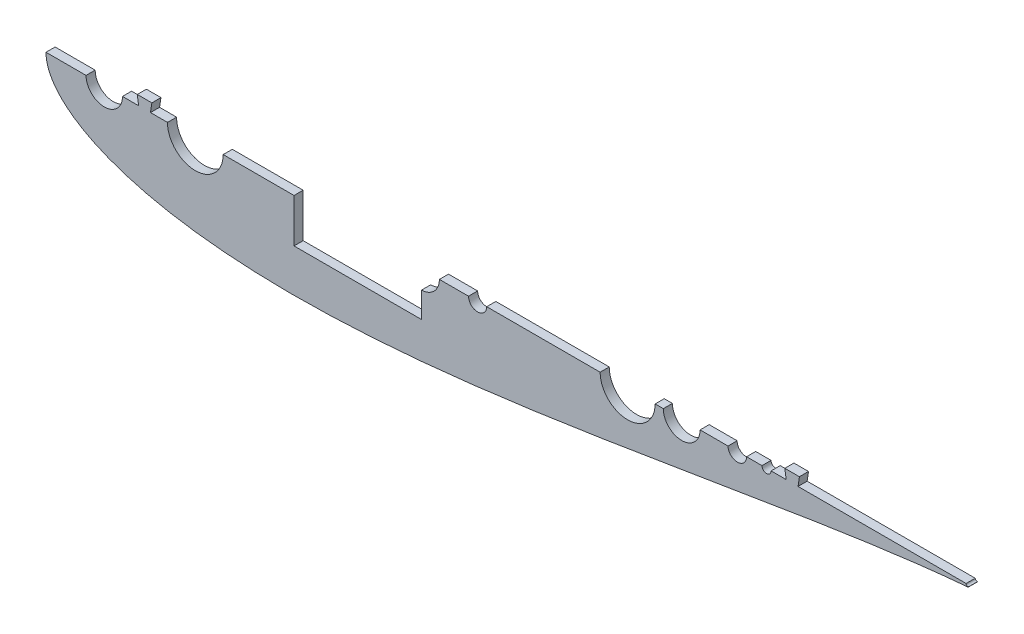
SolidWorks part; units mm, degrees
material "Beech"
ref_plane "Front Plane" through (0, 0, 0) normal (0, 0, 1) x (1, 0, 0)
ref_plane "Top Plane" through (0, 0, 0) normal (0, 1, 0) x (1, 0, 0)
ref_plane "Right Plane" through (0, 0, 0) normal (1, 0, 0) x (0, 0, -1)
curve "Curve4"
  spline degree 3 poles (100, 0, 0) (99.8498, 0.0023, 0) (99.4759, 0.008, 0) (99.1023, 0.0238, 0) (98.8789, 0.0332, 0) knots 0 0 0 0 0.401829 1 1 1 1
curve "Curve5"
  spline degree 3 poles (99.3714, -0.0082, 0) (100.2526, 0, 0) (99.3714, 0.0082, 0) (98.8504, 0.035, 0) (97.904, 0.0811, 0) (96.8285, 0.1543, 0) (95.5159, 0.2583, 0) (94.013, 0.3972, 0) (92.313, 0.574, 0) (90.4281, 0.791, 0) (88.3655, 1.0495, 0) (86.1348, 1.3497, 0) (83.7456, 1.691, 0) (81.2082, 2.0715, 0) (78.5335, 2.4886, 0) (75.7326, 2.9386, 0) (72.8172, 3.4168, 0) (69.799, 3.9177, 0) (66.6904, 4.435, 0) (63.5039, 4.9616, 0) (60.2521, 5.4899, 0) (56.948, 6.0119, 0) (53.6049, 6.519, 0) (50.2363, 7.0024, 0) (46.8558, 7.4534, 0) (43.4774, 7.8632, 0) (40.1152, 8.2232, 0) (36.7837, 8.5249, 0) (33.4975, 8.7606, 0) (30.2716, 8.923, 0) (27.1211, 9.0055, 0) (24.0614, 9.0025, 0) (21.108, 8.909, 0) (18.277, 8.7213, 0) (15.5843, 8.4369, 0) (13.0466, 8.0543, 0) (10.6806, 7.5735, 0) (8.5039, 6.996, 0) (6.5349, 6.3253, 0) (4.7933, 5.5673, 0) (3.3001, 4.7321, 0) (2.0777, 3.8366, 0) (1.1467, 2.91, 0) (0.5165, 2.0014, 0) (0.165, 1.1816, 0) (0.0231, 0.524, 0) (-0.0093, 0, 0) (0.0231, -0.524, 0) (0.165, -1.1816, 0) (0.5165, -2.0014, 0) (1.1467, -2.91, 0) (2.0777, -3.8366, 0) (3.3001, -4.7321, 0) (4.7933, -5.5673, 0) (6.5349, -6.3253, 0) (8.5039, -6.996, 0) (10.6806, -7.5735, 0) (13.0466, -8.0543, 0) (15.5843, -8.4369, 0) (18.277, -8.7213, 0) (21.108, -8.909, 0) (24.0614, -9.0025, 0) (27.1211, -9.0055, 0) (30.2716, -8.923, 0) (33.4975, -8.7606, 0) (36.7837, -8.5249, 0) (40.1152, -8.2232, 0) (43.4774, -7.8632, 0) (46.8558, -7.4534, 0) (50.2363, -7.0024, 0) (53.6049, -6.519, 0) (56.948, -6.0119, 0) (60.2521, -5.4899, 0) (63.5039, -4.9616, 0) (66.6904, -4.435, 0) (69.799, -3.9177, 0) (72.8172, -3.4168, 0) (75.7326, -2.9386, 0) (78.5335, -2.4886, 0) (81.2082, -2.0715, 0) (83.7456, -1.691, 0) (86.1348, -1.3497, 0) (88.3655, -1.0495, 0) (90.4281, -0.791, 0) (92.313, -0.574, 0) (94.013, -0.3972, 0) (95.5159, -0.2583, 0) (96.8285, -0.1543, 0) (97.904, -0.0811, 0) (98.8504, -0.035, 0) (99.3714, -0.0082, 0) (100.2526, 0, 0) (99.3714, 0.0082, 0) knots -0.009667 -0.005395 -0.002168 0 0.002168 0.005395 0.009667 0.014967 0.021271 0.028553 0.036781 0.04592 0.055932 0.066773 0.078397 0.090755 0.103793 0.117456 0.131686 0.146422 0.1616 0.177156 0.193024 0.209135 0.225421 0.241812 0.258238 0.274629 0.290914 0.307025 0.322893 0.338448 0.353626 0.368361 0.38259 0.396253 0.40929 0.421647 0.43327 0.444109 0.454119 0.463255 0.471479 0.478755 0.485052 0.490344 0.49461 0.497833 0.5 0.502167 0.50539 0.509656 0.514948 0.521245 0.528521 0.536745 0.545881 0.555891 0.56673 0.578353 0.59071 0.603747 0.61741 0.631639 0.646374 0.661552 0.677107 0.692975 0.709086 0.725371 0.741762 0.758188 0.774579 0.790865 0.806976 0.822844 0.8384 0.853578 0.868314 0.882544 0.896207 0.909245 0.921603 0.933227 0.944068 0.95408 0.963219 0.971447 0.978729 0.985033 0.990333 0.994605 0.997832 1 1.002168 1.005395 1.009667 periodic
sketch "Sketch2" plane through (0, 0, 0) normal (0, 0, 1) x (1, 0, 0)
  line L0 (100, 0) -> (0, 0) construction
  line L1 (1.2169, -991.9959) -> (1.2169, 49008.0041) construction
  line L2 (84.709, 0) -> (123.571, 0) construction
  line L3 (125.634, 0) -> (131.6629, 0) construction
  line L9 (0, 0) -> (643.9668, 0)
  line L13 (460.661, 0) -> (473.361, 0)
  circle A0 centre (104.14, 0) radius 19.431 construction
  arc A1 (1.2169, -4.6585) -> (1.2169, 4.6585) centre (9.525, 0) cw
  circle A4 centre (104.14, 0) radius 19.431
  circle A9 centre (40.64, 0) radius 12.7
  circle A14 centre (642.3793, 0) radius 1.5875 construction
  arc A15 (642.5108, -1.582) -> (642.5108, 1.582) centre (642.3793, 0) ccw
  spline S2 degree 3 poles (666.3448, -0.0547) (672.2538, 0) (666.3448, 0.0547) (662.8509, 0.2344) (656.505, 0.5436) (649.293, 1.0348) (640.4916, 1.7319) (630.4138, 2.6634) (619.0141, 3.8493) (606.375, 5.3044) (592.5439, 7.0376) (577.5855, 9.0506) (561.5643, 11.3389) (544.5497, 13.8907) (526.6141, 16.6877) (507.8326, 19.7051) (488.2827, 22.9117) (468.0444, 26.2704) (447.1994, 29.739) (425.8316, 33.2703) (404.0263, 36.8132) (381.8707, 40.3133) (359.4533, 43.7135) (336.8645, 46.9554) (314.1962, 49.9798) (291.5418, 52.7277) (268.9963, 55.1412) (246.6566, 57.1646) (224.6209, 58.7452) (202.9892, 59.8341) (181.8631, 60.3875) (161.3458, 60.367) (141.542, 59.7399) (122.5581, 58.4818) (104.5023, 56.5743) (87.485, 54.0089) (71.6197, 50.7848) (57.0237, 46.9125) (43.8205, 42.415) (32.1416, 37.3322) (22.1291, 31.7315) (13.9324, 25.7264) (7.6896, 19.5132) (3.4631, 13.4204) (1.1063, 7.9234) (0.1546, 3.5138) (-0.0622, 0) (0.1546, -3.5138) (1.1063, -7.9234) (3.4631, -13.4204) (7.6896, -19.5132) (13.9324, -25.7264) (22.1291, -31.7315) (32.1416, -37.3322) (43.8205, -42.415) (57.0237, -46.9125) (71.6197, -50.7848) (87.485, -54.0089) (104.5023, -56.5743) (122.5581, -58.4818) (141.542, -59.7399) (161.3458, -60.367) (181.8631, -60.3875) (202.9892, -59.8341) (224.6209, -58.7452) (246.6566, -57.1646) (268.9963, -55.1412) (291.5418, -52.7277) (314.1962, -49.9798) (336.8645, -46.9554) (359.4533, -43.7135) (381.8707, -40.3133) (404.0263, -36.8132) (425.8316, -33.2703) (447.1994, -29.739) (468.0444, -26.2704) (488.2827, -22.9117) (507.8326, -19.7051) (526.6141, -16.6877) (544.5497, -13.8907) (561.5643, -11.3389) (577.5855, -9.0506) (592.5439, -7.0376) (606.375, -5.3044) (619.0141, -3.8493) (630.4138, -2.6634) (640.4916, -1.7319) (649.293, -1.0348) (656.505, -0.5436) (662.8509, -0.2344) (666.3448, -0.0547) (672.2538, 0) (666.3448, 0.0547) knots -0.009667 -0.005395 -0.002168 0 0.002168 0.005395 0.009667 0.014967 0.021271 0.028553 0.036781 0.04592 0.055932 0.066773 0.078397 0.090755 0.103793 0.117456 0.131686 0.146422 0.1616 0.177156 0.193024 0.209135 0.225421 0.241812 0.258238 0.274629 0.290914 0.307025 0.322893 0.338448 0.353626 0.368361 0.38259 0.396253 0.40929 0.421647 0.43327 0.444109 0.454119 0.463255 0.471479 0.478755 0.485052 0.490344 0.49461 0.497833 0.5 0.502167 0.50539 0.509656 0.514948 0.521245 0.528521 0.536745 0.545881 0.555891 0.56673 0.578353 0.59071 0.603747 0.61741 0.631639 0.646374 0.661552 0.677107 0.692975 0.709086 0.725371 0.741762 0.758188 0.774579 0.790865 0.806976 0.822844 0.8384 0.853578 0.868314 0.882544 0.896207 0.909245 0.921603 0.933227 0.944068 0.95408 0.963219 0.971447 0.978729 0.985033 0.990333 0.994605 0.997832 1 1.002168 1.005395 1.009667 only from (670.56, 0) to (670.56, 0)
  point P2 (167.64, 0)
  point P8 (1.2169, -4.6585)
  point P10 (1.2169, 4.6585)
  point P28 (133.9182, 0)
  point P49 (130.0977, 0)
  point P59 (95.1064, 0)
  dimension "D2" = 38.862
  dimension "D8" = 25.4
  dimension "D9" = 63.5
  dimension "D10" = 3.175
  dimension "D1" = 167.64
  dimension "D6" = 63.5
extrude "Boss-Extrude1" add sketch "Sketch2" along normal blind 6.35
sketch "Sketch3" plane through (0, 0, 6.35) normal (0, 0, 1) x (1, 0, 0)
  line L0 (84.14, -12.7) -> (62.637, -12.7) construction
  line L1 (430.4749, -1041.2705) -> (430.4749, 48958.7295) construction
  line L2 (123.571, 0) -> (643.9668, 0) construction
  line L3 (27.94, 0) -> (0, 0)
  line L4 (643.9668, 0) -> (123.571, 0)
  line L5 (84.709, 0) -> (53.34, 0)
  line L6 (27.94, 0) -> (0, 0)
  line L7 (221.3683, -1000) -> (221.3683, 49000) construction
  line L8 (84.709, 0) -> (53.34, 0)
  line L9 (232.7983, -1000) -> (232.7983, 49000) construction
  line L10 (307.8396, -1000) -> (307.8396, 49000) construction
  line L11 (319.2696, -1000) -> (319.2696, 49000) construction
  line L12 (374.9948, -1000) -> (374.9948, 49000) construction
  line L13 (84.709, -17.145) -> (65.0689, -17.145) construction
  line L14 (424.7788, -1000) -> (424.7788, 49000) construction
  line L15 (135.001, -1000) -> (135.001, 49000) construction
  line L16 (386.4248, -1000) -> (386.4248, 49000) construction
  line L17 (52.7726, -27.2676) -> (52.7726, -27.2676) construction
  arc A0 (36.4352, -25.0495) -> (62.637, -12.7) centre (40.64, 0) ccw construction
  circle A1 centre (502.475, 0) radius 3.175
  circle A2 centre (178.1847, 0) radius 43.1837
  arc A3 (642.5108, -1.582) -> (643.9668, 0) centre (642.3793, 0) ccw
  arc A4 (84.709, 0) -> (123.571, 0) centre (104.14, 0) ccw
  arc A5 (27.94, 0) -> (53.34, 0) centre (40.64, 0) ccw
  arc A6 (642.5108, -1.582) -> (643.9668, 0) centre (642.3793, 0) ccw
  circle A7 centre (270.319, 0) radius 37.5206
  arc A8 (27.94, 0) -> (53.34, 0) centre (40.64, 0) ccw
  circle A9 centre (347.1322, 0) radius 27.8626
  circle A10 centre (405.6018, 0) radius 19.177
  circle A11 centre (443.3019, 0) radius 12.827
  circle A12 centre (482.0825, 0) radius 6.477
  arc A13 (52.7726, -27.2676) -> (65.0689, -17.145) centre (40.64, 0) ccw construction
  arc A14 (635.7346, 15.0394) -> (635.7346, 15.0394) centre (635.7346, 15.0394) ccw construction
  circle A15 centre (300.99, 0) radius 6.35
  arc A16 (84.709, 0) -> (123.571, 0) centre (104.14, 0) ccw construction
  circle A17 centre (261.62, 0) radius 12.7
  arc A18 (84.709, 0) -> (123.571, 0) centre (104.14, 0) ccw construction
  spline S1 degree 3 poles (1868.8296, -3504.7019) (382.5713, 207.4774) (-16.9965, 75.9519) (1.1063, -7.9234) (3.4631, -13.4204) (7.6896, -19.5132) (13.9324, -25.7264) (22.1291, -31.7315) (32.1416, -37.3322) (43.8205, -42.415) (57.0237, -46.9125) (71.6197, -50.7848) (87.485, -54.0089) (104.5023, -56.5743) (122.5581, -58.4818) (141.542, -59.7399) (161.3458, -60.367) (181.8631, -60.3875) (202.9892, -59.8341) (224.6209, -58.7452) (246.6566, -57.1646) (268.9963, -55.1412) (291.5418, -52.7277) (314.1962, -49.9798) (336.8645, -46.9554) (359.4533, -43.7135) (381.8707, -40.3133) (404.0263, -36.8132) (425.8316, -33.2703) (447.1994, -29.739) (468.0444, -26.2704) (488.2827, -22.9117) (507.8326, -19.7051) (526.6141, -16.6877) (544.5497, -13.8907) (561.5643, -11.3389) (577.5855, -9.0506) (592.5439, -7.0376) (606.375, -5.3044) (619.0141, -3.8493) (630.4138, -2.6634) (765.6289, 9.8343) (921.2001, -12.4783) (-3340.3196, -367.5446) knots 0.325989 0.325989 0.325989 0.325989 0.502167 0.50539 0.509656 0.514948 0.521245 0.528521 0.536745 0.545881 0.555891 0.56673 0.578353 0.59071 0.603747 0.61741 0.631639 0.646374 0.661552 0.677107 0.692975 0.709086 0.725371 0.741762 0.758188 0.774579 0.790865 0.806976 0.822844 0.8384 0.853578 0.868314 0.882544 0.896207 0.909245 0.921603 0.933227 0.944068 0.95408 0.963219 0.971447 0.978729 1.255901 1.255901 1.255901 1.255901 only from (0, 0) to (642.5108, -1.582)
  spline S2 degree 3 poles (0, 0) (0, -1.0075) (0.1546, -3.5138) (1.1063, -7.9234) (3.4631, -13.4204) (7.6896, -19.5132) (13.9324, -25.7264) (22.1291, -31.7315) (32.1416, -37.3322) (43.8205, -42.415) (57.0237, -46.9125) (71.6197, -50.7848) (87.485, -54.0089) (104.5023, -56.5743) (122.5581, -58.4818) (141.542, -59.7399) (161.3458, -60.367) (181.8631, -60.3875) (202.9892, -59.8341) (224.6209, -58.7452) (246.6566, -57.1646) (268.9963, -55.1412) (291.5418, -52.7277) (314.1962, -49.9798) (336.8645, -46.9554) (359.4533, -43.7135) (381.8707, -40.3133) (404.0263, -36.8132) (425.8316, -33.2703) (447.1994, -29.739) (468.0444, -26.2704) (488.2827, -22.9117) (507.8326, -19.7051) (526.6141, -16.6877) (544.5497, -13.8907) (561.5643, -11.3389) (577.5855, -9.0506) (592.5439, -7.0376) (606.375, -5.3044) (619.0141, -3.8493) (630.4138, -2.6634) (638.0937, -1.9535) (641.9934, -1.6251) (642.5108, -1.582) knots 0.5 0.5 0.5 0.5 0.502167 0.50539 0.509656 0.514948 0.521245 0.528521 0.536745 0.545881 0.555891 0.56673 0.578353 0.59071 0.603747 0.61741 0.631639 0.646374 0.661552 0.677107 0.692975 0.709086 0.725371 0.741762 0.758188 0.774579 0.790865 0.806976 0.822844 0.8384 0.853578 0.868314 0.882544 0.896207 0.909245 0.921603 0.933227 0.944068 0.95408 0.963219 0.971447 0.978729 0.979843 0.979843 0.979843 0.979843
  spline S4 degree 1 poles (52.7726, -27.2676) (635.7346, 15.0394) knots 0 0 1 1 construction
  spline S5 degree 3 poles (52.7726, -27.2676) (54.0926, -27.7489) (56.7366, -28.6728) (62.1406, -30.4123) (69.0328, -32.377) (77.4854, -34.4334) (88.9335, -36.8105) (103.518, -39.1624) (127.2195, -41.8192) (149.278, -42.9685) (171.4659, -43.2641) (184.6179, -43.147) (204.88, -42.6136) (230.6688, -41.2806) (259.5457, -38.8537) (285.4896, -36.1548) (308.0845, -33.483) (336.7884, -29.6901) (371.8957, -24.5635) (406.3553, -19.0892) (434.738, -14.4252) (452.3886, -11.4946) (466.3773, -9.1682) (477.5482, -7.3138) (486.443, -5.8439) (493.0571, -4.7561) (499.6739, -3.672) (509.9177, -2.0047) (530.825, 1.3479) (560.813, 5.9575) (591.8594, 10.2336) (616.8444, 13.1905) (629.4403, 14.4712) (635.7346, 15.0394) knots 0.548481 0.548481 0.548481 0.548481 0.551822 0.555162 0.561843 0.568525 0.575206 0.588568 0.601931 0.628656 0.63757 0.650932 0.657614 0.682106 0.70749 0.720853 0.738901 0.756948 0.783673 0.81573 0.832326 0.845688 0.854263 0.862837 0.870035 0.873634 0.877233 0.88443 0.895905 0.92263 0.949355 0.962718 0.97608 0.97608 0.97608 0.97608 construction
  line M19 (643.9668, 0) -> (123.571, 0)
  dimension "D3" = 11.43
  dimension "D7" = 38.354
  dimension "D8" = 25.654
  dimension "D9" = 12.954
  dimension "D2" = 6.35
  dimension "D11" = 12.7
  dimension "D13" = 25.4
  dimension "D4" = 11.43
  dimension "D5" = 11.43
  dimension "D6" = 11.43
  dimension "D12" = 196.85
  dimension "D14" = 157.48
  dimension "D1" = 0
  dimension "D10" = 17.145
extrude "Cut-Extrude2" cut sketch "Sketch3" against normal through all both and the other way through all contours A10 M19 | A11 M19 | A12 M19 | A1 M19 | A17 M19 | A15 M19
sketch "Sketch4" plane through (0, 0, 6.35) normal (0, 0, 1) x (1, 0, 0)
  line L0 (63.66, 6.35) -> (73.82, 6.35)
  line L1 (65.565, 6.35) -> (71.915, 6.35)
  line L2 (65.565, 6.35) -> (65.565, -6.35)
  line L3 (65.565, -6.35) -> (71.915, -6.35)
  line L4 (71.915, 6.35) -> (71.915, -6.35)
  line L5 (65.565, 6.35) -> (71.915, -6.35) construction
  line L6 (65.565, -6.35) -> (71.915, 6.35) construction
  line L7 (71.915, -6.35) -> (73.82, 6.35)
  line L8 (63.66, 6.35) -> (65.565, -6.35)
  line L9 (248.92, 0) -> (123.571, 0)
  line L17 (248.92, 0) -> (123.571, 0)
  line L18 (499.3, 0) -> (488.5595, 0)
  line L19 (499.3, 0) -> (488.5595, 0)
  line L22 (84.709, 0) -> (53.34, 0)
  line L23 (84.709, 0) -> (53.34, 0)
  line L24 (27.94, 0) -> (0, 0)
  line L25 (27.94, 0) -> (0, 0)
  line L26 (643.9668, 0) -> (505.65, 0)
  line L27 (515.2295, 6.35) -> (525.3895, 6.35)
  line L28 (517.1345, 6.35) -> (523.4845, 6.35)
  line L29 (517.1345, 6.35) -> (517.1345, -6.35)
  line L30 (517.1345, -6.35) -> (523.4845, -6.35)
  line L31 (523.4845, 6.35) -> (523.4845, -6.35)
  line L32 (517.1345, 6.35) -> (523.4845, -6.35) construction
  line L33 (517.1345, -6.35) -> (523.4845, 6.35) construction
  line L34 (517.1345, -6.35) -> (515.2295, 6.35)
  line L35 (523.4845, -6.35) -> (525.3895, 6.35)
  line L36 (643.9668, 0) -> (505.65, 0)
  line L37 (475.6055, 0) -> (456.1289, 0)
  line L38 (475.6055, 0) -> (456.1289, 0)
  line L39 (430.4749, 0) -> (424.7788, 0)
  line L40 (430.4749, 0) -> (424.7788, 0)
  line L41 (386.4248, 0) -> (307.34, 0)
  line L42 (386.4248, 0) -> (307.34, 0)
  line L43 (294.64, 0) -> (274.32, 0)
  line L44 (294.64, 0) -> (274.32, 0)
  arc A7 (499.3, 0) -> (505.65, 0) centre (502.475, 0) ccw
  arc A8 (499.3, 0) -> (505.65, 0) centre (502.475, 0) ccw
  arc A11 (294.64, 0) -> (307.34, 0) centre (300.99, 0) ccw
  arc A12 (294.64, 0) -> (307.34, 0) centre (300.99, 0) ccw
  arc A13 (84.709, 0) -> (123.571, 0) centre (104.14, 0) ccw
  arc A14 (84.709, 0) -> (123.571, 0) centre (104.14, 0) ccw
  arc A15 (27.94, 0) -> (53.34, 0) centre (40.64, 0) ccw
  arc A16 (386.4248, 0) -> (424.7788, 0) centre (405.6018, 0) ccw
  arc A17 (27.94, 0) -> (53.34, 0) centre (40.64, 0) ccw
  arc A18 (642.5108, -1.582) -> (643.9668, 0) centre (642.3793, 0) ccw
  arc A19 (642.5108, -1.582) -> (643.9668, 0) centre (642.3793, 0) ccw
  arc A20 (475.6055, 0) -> (488.5595, 0) centre (482.0825, 0) ccw
  arc A21 (475.6055, 0) -> (488.5595, 0) centre (482.0825, 0) ccw
  arc A22 (430.4749, 0) -> (456.1289, 0) centre (443.3019, 0) ccw
  arc A23 (430.4749, 0) -> (456.1289, 0) centre (443.3019, 0) ccw
  arc A24 (248.92, 0) -> (274.32, 0) centre (261.62, 0) ccw
  arc A25 (386.4248, 0) -> (424.7788, 0) centre (405.6018, 0) ccw
  arc A26 (248.92, 0) -> (274.32, 0) centre (261.62, 0) ccw
  spline S1 degree 3 poles (1083.539, -1665.6175) (237.9838, 156.2926) (-13.4194, 59.3783) (1.1063, -7.9234) (3.4631, -13.4204) (7.6896, -19.5132) (13.9324, -25.7264) (22.1291, -31.7315) (32.1416, -37.3322) (43.8205, -42.415) (57.0237, -46.9125) (71.6197, -50.7848) (87.485, -54.0089) (104.5023, -56.5743) (122.5581, -58.4818) (141.542, -59.7399) (161.3458, -60.367) (181.8631, -60.3875) (202.9892, -59.8341) (224.6209, -58.7452) (246.6566, -57.1646) (268.9963, -55.1412) (291.5418, -52.7277) (314.1962, -49.9798) (336.8645, -46.9554) (359.4533, -43.7135) (381.8707, -40.3133) (404.0263, -36.8132) (425.8316, -33.2703) (447.1994, -29.739) (468.0444, -26.2704) (488.2827, -22.9117) (507.8326, -19.7051) (526.6141, -16.6877) (544.5497, -13.8907) (561.5643, -11.3389) (577.5855, -9.0506) (592.5439, -7.0376) (606.375, -5.3044) (619.0141, -3.8493) (630.4138, -2.6634) (741.1247, 7.5694) (864.0226, -5.3554) (-1347.5502, -198.2161) knots 0.362281 0.362281 0.362281 0.362281 0.502167 0.50539 0.509656 0.514948 0.521245 0.528521 0.536745 0.545881 0.555891 0.56673 0.578353 0.59071 0.603747 0.61741 0.631639 0.646374 0.661552 0.677107 0.692975 0.709086 0.725371 0.741762 0.758188 0.774579 0.790865 0.806976 0.822844 0.8384 0.853578 0.868314 0.882544 0.896207 0.909245 0.921603 0.933227 0.944068 0.95408 0.963219 0.971447 0.978729 1.20286 1.20286 1.20286 1.20286 only from (0, 0) to (642.5108, -1.582)
  spline S2 degree 3 poles (0, 0) (0, -1.0075) (0.1546, -3.5138) (1.1063, -7.9234) (3.4631, -13.4204) (7.6896, -19.5132) (13.9324, -25.7264) (22.1291, -31.7315) (32.1416, -37.3322) (43.8205, -42.415) (57.0237, -46.9125) (71.6197, -50.7848) (87.485, -54.0089) (104.5023, -56.5743) (122.5581, -58.4818) (141.542, -59.7399) (161.3458, -60.367) (181.8631, -60.3875) (202.9892, -59.8341) (224.6209, -58.7452) (246.6566, -57.1646) (268.9963, -55.1412) (291.5418, -52.7277) (314.1962, -49.9798) (336.8645, -46.9554) (359.4533, -43.7135) (381.8707, -40.3133) (404.0263, -36.8132) (425.8316, -33.2703) (447.1994, -29.739) (468.0444, -26.2704) (488.2827, -22.9117) (507.8326, -19.7051) (526.6141, -16.6877) (544.5497, -13.8907) (561.5643, -11.3389) (577.5855, -9.0506) (592.5439, -7.0376) (606.375, -5.3044) (619.0141, -3.8493) (630.4138, -2.6634) (638.0937, -1.9535) (641.9934, -1.6251) (642.5108, -1.582) knots 0.5 0.5 0.5 0.5 0.502167 0.50539 0.509656 0.514948 0.521245 0.528521 0.536745 0.545881 0.555891 0.56673 0.578353 0.59071 0.603747 0.61741 0.631639 0.646374 0.661552 0.677107 0.692975 0.709086 0.725371 0.741762 0.758188 0.774579 0.790865 0.806976 0.822844 0.8384 0.853578 0.868314 0.882544 0.896207 0.909245 0.921603 0.933227 0.944068 0.95408 0.963219 0.971447 0.978729 0.979843 0.979843 0.979843 0.979843
  point P0 (68.74, 0)
  point P15 (68.74, 6.35)
  point P25 (68.74, 6.35)
  point P37 (520.3095, 0)
  point P44 (520.3095, 6.35)
  point P45 (520.3095, 6.35)
  line M32 (84.709, 0) -> (53.34, 0)
  dimension "D2" = 6.35
  dimension "D3" = 10.16
  dimension "D4" = 12.7
  dimension "D5" = 6.35
  dimension "D6" = 12.7
  dimension "D7" = 31.75
  dimension "D8" = 10.16
  dimension "D1" = 0
extrude "Boss-Extrude2" add sketch "Sketch4" against normal up to surface (6.35 mm away) contours L34 L36 L29 L27 | L31 L27 L29 L36 | L36 L35 L27 L31 | L0 L8 L2 M32 | L4 L0 L2 M32 | L7 L0 L4 M32 up to face at (318.2754, -4.9427, 0)
sketch "Sketch5" plane through (0, 0, 6.35) normal (0, 0, 1) x (1, 0, 0)
  text T0 "Servo Access Airfoil" font "Century Gothic" height 5.08
extrude "Cut-Extrude4" cut sketch "Sketch7" against normal through all
sketch "Sketch7" plane through (327.9592, -13.7514, 6.35) normal (0, 0, 1) x (1, 0, 0)
  line L1 (-154.9852, -16.7286) -> (-66.0852, -16.7286)
  line L2 (-154.9852, -16.7286) -> (-154.9852, 44.2314)
  line L3 (-154.9852, 44.2314) -> (-66.0852, 44.2314)
  line L4 (-66.0852, -16.7286) -> (-66.0852, 44.2314)
  line L5 (-154.9852, -16.7286) -> (-66.0852, 44.2314) construction
  line L6 (-154.9852, 44.2314) -> (-66.0852, -16.7286) construction
  point P0 (-110.5352, 13.7514)
extrude "Cut-Extrude5" cut sketch "Sketch8" against normal through all
sketch "Sketch8" plane through (327.9592, -13.7514, 6.35) normal (0, 0, 1) x (1, 0, 0)
  circle A0 centre (314.9285, 13.7514) radius 1.2446
equation "\"0.5n\"=0"
